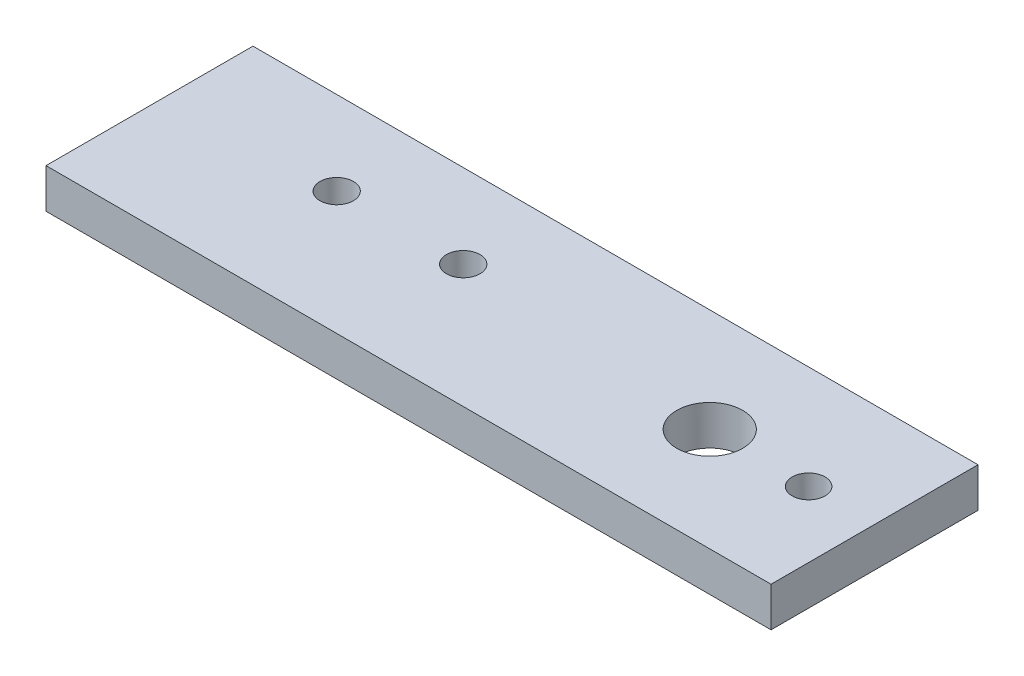
SolidWorks part; units mm, degrees
ref_plane "Front Plane" through (0, 0, 0) normal (0, 0, 1) x (1, 0, 0)
ref_plane "Top Plane" through (0, 0, 0) normal (0, 1, 0) x (1, 0, 0)
ref_plane "Right Plane" through (0, 0, 0) normal (1, 0, 0) x (0, 0, -1)
sketch "Sketch1" plane through (0, 0, 0) normal (0, 1, 0) x (1, 0, 0)
  line L6 (-55, -15.7) -> (55, -15.7)
  line L8 (-55, -15.7) -> (-55, 15.7)
  line L14 (-55, 15.7) -> (55, 15.7)
  line L15 (55, -15.7) -> (55, 15.7)
  line L16 (-55, -15.7) -> (55, 15.7) construction
  line L17 (-55, 15.7) -> (55, -15.7) construction
  point P0 (0, 0)
  dimension "D1" = 31.4
  dimension "D2" = 110
extrude "Boss-Extrude1" add sketch "Sketch1" along normal blind 6
sketch "Sketch2" plane through (0, 6, 0) normal (0, 1, 0) x (1, 0, 0)
  line L0 (-55, 3) -> (-29.6, 3) construction
  line L1 (15, -9.7) -> (-55, -9.7) construction
  line L2 (15, -9.7) -> (15, 15.7) construction
  line L3 (15, 15.7) -> (-55, 15.7) construction
  line L4 (-55, -9.7) -> (-55, 15.7) construction
  line L5 (15, -9.7) -> (-55, 15.7) construction
  line L6 (15, 15.7) -> (-55, -9.7) construction
  line L7 (15, 3) -> (-10.4, 3) construction
  line L8 (45, 0) -> (55, 0) construction
  line L9 (30, 0) -> (45, 0) construction
  line L10 (55, -15.7) -> (55, 15.7) construction
  circle A0 centre (-10.4, 3) radius 2.54
  circle A1 centre (-29.6, 3) radius 2.54
  circle A2 centre (30, 0) radius 5
  circle A3 centre (45, 0) radius 2.5
  point P0 (-20, 3)
  dimension "D4" = 5.08
  dimension "D5" = 10
  dimension "D8" = 5
  dimension "D1" = 25.4
  dimension "D2" = 70
  dimension "D3" = 25.4
  dimension "D6" = 15
  dimension "D7" = 15
extrude "Cut-Extrude1" cut sketch "Sketch2" against normal through all both and the other way through all
equation "\"testbed_height\" = 91.50mm"
equation "\"plate_thickness\" = 6mm"
equation "\"main_body_splay_length\" = 48.5mm"
equation "\"splay_shaft_length_no_wires\" = 10mm"
equation "\"splay_shaft_length_wires\" = 6.5mm"
equation "\"timing_pulley_offset\" = 0mm"
equation "\"effective_motor_length\" = \"timing_pulley_offset\" + \"splay_shaft_length_no_wires\" + \"main_body_splay_length\""
equation "\"80_20_side\" = 25.4mm"
equation "\"80_20_length\" = 152.4mm"
equation "\"80_20_optic_mount_length\" = \"80_20_length\" - 25.4mm"
equation "\"optic_board_hole_size\" = 6.35mm"
equation "\"total_mounting_length\" = \"testbed_height\" - \"effective_motor_length\" - \"80_20_side\""
equation "\"mounting_vertical_portion_height\" = \"total_mounting_length\" - 2 * \"plate_thickness\""
equation "\"face_mount_width\" = 15.25mm"
equation "\"center_dist_to_face_mount_vertical_screws\" = 5mm"
equation "\"D1@Boss-Extrude1\"=\"plate_thickness\""
